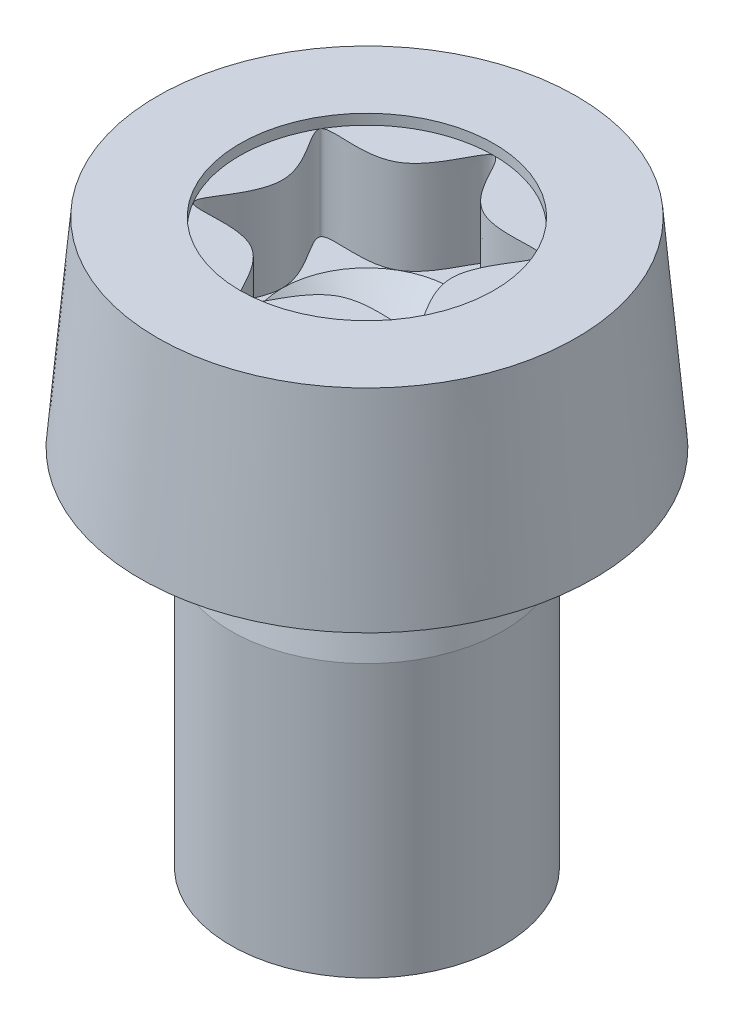
SolidWorks part; units mm, degrees
material "AISI 316L Acero inoxidable"
ref_plane "Front" through (0, 0, 0) normal (0, 0, 1) x (1, 0, 0)
ref_plane "Top" through (0, 0, 0) normal (0, 1, 0) x (1, 0, 0)
ref_plane "Right" through (0, 0, 0) normal (1, 0, 0) x (0, 0, -1)
sketch "Sketch1" plane through (0, 0, 0) normal (0, 0, 1) x (1, 0, 0)
  line L0 (0, 0) -> (0, 5.1006) construction
  line L1 (0, 12.4) -> (4.615, 12.4)
  line L2 (4.615, 12.4) -> (5, 8)
  line L3 (5, 8) -> (3, 8)
  line L4 (3, 0) -> (3, 6)
  line L5 (3, 0) -> (0, 0)
  line L6 (0, 0) -> (0, 12.4)
  line L7 (5, 8) -> (5, 7) construction
  line L8 (3, 6) -> (2.6, 8)
  line L9 (2.6, 8) -> (3, 8)
  line L10 (5, 7) -> (5, 1) construction
  dimension "length" = 8
  dimension "head_ht" = 4.4
  dimension "head_dia" = 10
  dimension "dia" = 6
  dimension "D1" = 5
  dimension "pitch" = 1
  dimension "thread_gap" = 2
  dimension "D2" = 0.4
  dimension "thread_length" = 6
revolve "Body-Revolve" add sketch "Sketch1" angle 360 about L0
cosmetic thread "ThreadCosmetic" [suppressed] parameters "D1"=6, "D2"=4.9175
fillet "Fillet1" radius 0.25 1 edges at (0, 8, -2.6)
sketch "Sketch2" plane through (0, 12.4, 0) normal (0, 1, 0) x (-1, 0, 0)
  line L0 (0, -3.08) -> (0, 0)
  line L1 (0, 0) -> (-1.4, -2.4249)
  circle A0 centre (0, 0) radius 2.8
  circle A1 centre (0, 0) radius 1.8667
  spline S0 degree 3 poles (0.6039, -1.046) (0, -3.677) (-0.6039, -1.046) (-3.1844, -1.8385) (-1.2078, 0) (-3.1844, 1.8385) (-0.6039, 1.046) (0, 3.677) (0.6039, 1.046) (3.1844, 1.8385) (1.2078, 0) (3.1844, -1.8385) (0.6039, -1.046) (0, -3.677) (-0.6039, -1.046) knots -0.25 -0.166667 -0.083333 0 0.083333 0.166667 0.25 0.333333 0.416667 0.5 0.583333 0.666667 0.75 0.833333 0.916667 1 1.083333 1.166667 1.25 only from (0, -2.8) to (0, -2.8)
  point P5 (0, -2.8)
  point P7 (-0.9333, -1.6166)
  point P10 (-2.4249, -1.4)
  point P11 (-2.4249, 1.4)
  point P12 (0, 2.8)
  point P13 (2.4249, 1.4)
  point P14 (2.4249, -1.4)
  point P15 (-1.8667, 0)
  point P16 (-0.9333, 1.6166)
  point P17 (0.9333, 1.6166)
  point P18 (1.8667, 0)
  point P19 (0.9333, -1.6166)
  dimension "socket_dia" = 5.6
  dimension "D1" = 3.7333
  dimension "D2" = 3.08
  dimension "D3" = 30
extrude "Socket-Cut-Extrude1" cut sketch "Sketch2" against normal blind 2.29 contours S0
sketch "Sketch3" plane through (0, 12.4, 0) normal (0, 1, 0) x (-1, 0, 0)
  circle A0 centre (0, 0) radius 2.8
  dimension "D1" = 5.6
extrude "Socket-Cut-Extrude2" cut sketch "Sketch3" against normal blind 0.229
sketch "Sketch4" plane through (0, 0, 0) normal (0, 0, 1) x (1, 0, 0)
  line L0 (0, 10.11) -> (1.8667, 10.11)
  line L1 (2.4353, 10.11) -> (-2.4353, 10.11) construction
  line L2 (1.8667, 10.11) -> (0, 8.44)
  line L3 (0, 0) -> (0, 5.1006) construction
  line L4 (0, 8.44) -> (0, 10.11)
  line L5 (2.8, 12.4) -> (-2.8, 12.4) construction
  dimension "D1" = 3.96
  dimension "D2" = 1.8667
revolve "Drill-Cut-Revolve" cut sketch "Sketch4" angle 360 about axis through (0, 0, 0) along (0, 1, 0)
sketch "Sketch5" plane through (0, 0, 0) normal (0, 0, 1) x (1, 0, 0)
  line L0 (3, 0) -> (2.4588, 0.3125)
  line L1 (2.4588, 0.3125) -> (3, 0.625)
  line L2 (3, 0) -> (3, 6) construction
  line L3 (3, 0.625) -> (3, 0)
  line L4 (0, 0) -> (0, 5.1006) construction
  dimension "D1" = 2.4588
revolve "ThreadSchematic" [suppressed] cut sketch "Sketch5" angle 360 about axis through (0, 0, 0) along (0, 1, 0)
pattern_linear "ThdSchPat" [suppressed] count 6 spacing 1 along (0, 1, 0)
equation "\"D2@Sketch1\" = 0.2*\"thread_gap@Sketch1\""
equation "\"D1@Sketch2\" = \"socket_dia@Sketch2\" / 1.5"
equation "\"D2@Sketch2\" = \"socket_dia@Sketch2\" / 2 * 1.1"
equation "\"D1@Sketch3\" =\"socket_dia@Sketch2\""
equation "\"D1@Socket-Cut-Extrude2\" = .1 * \"socket_dep@Socket-Cut-Extrude1\""
equation "\"D1@Sketch4\" = 0.9*\"head_ht@Sketch1\""
equation "\"D2@Sketch4\" = \"D1@Sketch2\" / 2"
equation "\"D1@ThreadCosmetic\" = \"thread_length@Sketch1\""
equation "\"D2@ThreadCosmetic\" = \"dia@Sketch1\" - 1.0825 * \"pitch@Sketch1\""
equation "\"D1@Sketch5\" = \"D2@ThreadCosmetic\" / 2"
equation "\"D3@ThdSchPat\" = \"pitch@Sketch1\""
equation "\"D1@ThdSchPat\" = \"thread_length@Sketch1\" / \"pitch@Sketch1\""
